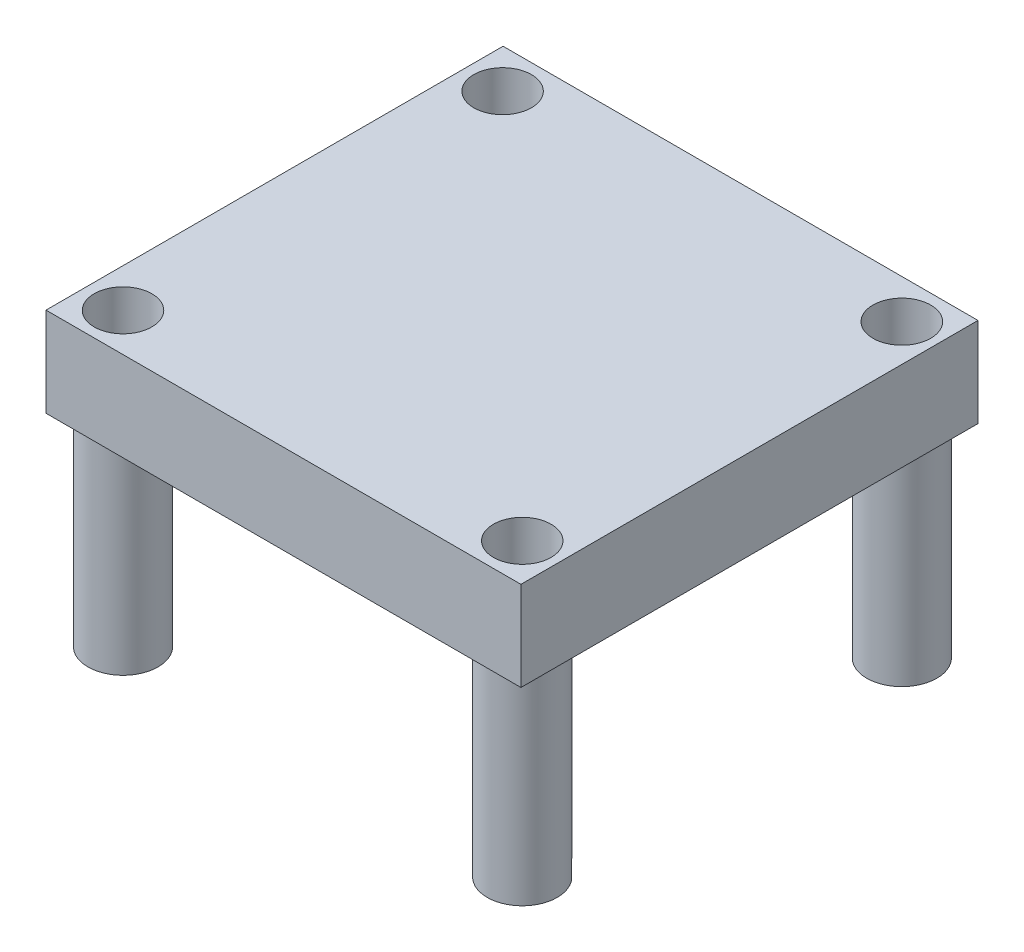
SolidWorks part; units mm, degrees
ref_plane "Front Plane" through (0, 0, 0) normal (0, 0, 1) x (1, 0, 0)
ref_plane "Top Plane" through (0, 0, 0) normal (0, 1, 0) x (1, 0, 0)
ref_plane "Right Plane" through (0, 0, 0) normal (1, 0, 0) x (0, 0, -1)
sketch "Sketch1" plane through (0, 0, 0) normal (0, 1, 0) x (1, 0, 0)
  line L1 (-11.2829, 10.6292) -> (15.7173, 10.6292)
  line L2 (-11.2829, 10.6292) -> (-11.2829, -15.355)
  line L3 (-11.2829, -15.355) -> (15.7173, -15.355)
  line L4 (15.7173, 10.6292) -> (15.7173, -15.355)
  dimension "D1" = 27.0002
  dimension "D2" = 25.9842
extrude "Boss-Extrude1" add sketch "Sketch1" along normal blind 5.08
sketch "Sketch2" plane through (0, 0, 0) normal (0, -1, 0) x (1, 0, 0)
  circle A0 centre (-9.0827, 13.1767) radius 1.9939
  circle A1 centre (13.6127, 13.1767) radius 1.9939
  circle A2 centre (-9.0827, -8.4031) radius 1.9939
  circle A3 centre (13.6127, -8.4031) radius 1.9939
  circle A4 centre (-9.0827, 13.1767) radius 1.6383
  circle A5 centre (-9.0827, -8.4031) radius 1.6383
  circle A6 centre (13.6127, 13.1767) radius 1.6383
  circle A7 centre (13.6127, -8.4031) radius 1.6383
  point P8 (-9.0827, -8.2915)
  point P13 (13.7243, 13.1767)
  point P15 (13.5012, -8.4031)
  dimension "D1" = 3.9878
  dimension "D2" = 3.2766
extrude "Boss-Extrude2" add sketch "Sketch2" along normal blind 11.4808
sketch "Sketch3" plane through (0, 5.08, 0) normal (0, 1, 0) x (1, 0, 0)
  circle A0 centre (13.6127, 8.4031) radius 1.6416
  circle A1 centre (-9.0827, 8.4031) radius 1.6383
  circle A2 centre (13.6127, -13.1767) radius 1.6383
  circle A3 centre (-9.0827, -13.1767) radius 1.6383
extrude "Cut-Extrude1" cut sketch "Sketch3" against normal through all both
